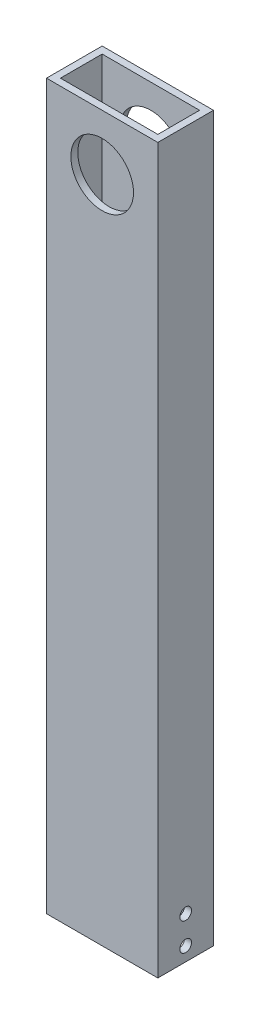
SolidWorks part; units mm, degrees
ref_plane "Front Plane" through (0, 0, 0) normal (0, 0, 1) x (1, 0, 0)
ref_plane "Top Plane" through (0, 0, 0) normal (0, 1, 0) x (1, 0, 0)
ref_plane "Right Plane" through (0, 0, 0) normal (1, 0, 0) x (0, 0, -1)
sketch "Sketch1" plane through (0, 0, 0) normal (0, 1, 0) x (1, 0, 0)
  line L1 (0, 0) -> (50.8, 0)
  line L2 (0, 0) -> (0, 25.4)
  line L3 (0, 25.4) -> (50.8, 25.4)
  line L4 (50.8, 0) -> (50.8, 25.4)
  line L5 (3.175, 3.175) -> (47.625, 3.175)
  line L6 (3.175, 3.175) -> (3.175, 22.225)
  line L7 (3.175, 22.225) -> (47.625, 22.225)
  line L8 (47.625, 3.175) -> (47.625, 22.225)
  dimension "D1" = 3.175
  dimension "D2" = 3.175
  dimension "D3" = 3.175
  dimension "D4" = 3.175
  dimension "D5" = 25.4
  dimension "D6" = 50.8
extrude "Boss-Extrude2" add sketch "Sketch1" along normal blind 330.2
sketch "Sketch2" plane through (0, 0, 0) normal (0, 0, 1) x (1, 0, 0)
  line L0 (0, 330.2) -> (0, 0) construction
  line L1 (0, 330.2) -> (50.8, 330.2) construction
  circle A0 centre (25.4, 304.8) radius 14.2875
  dimension "D3" = 28.575
  dimension "D1" = 25.4
  dimension "D2" = 25.4
extrude "Cut-Extrude1" cut sketch "Sketch2" against normal up to surface (25.4 mm away) contours A0 up to face at (25.4, 165.1, -25.4)
sketch "Sketch3" plane through (50.8, 0, 0) normal (1, 0, 0) x (0, 0, -1)
  line L0 (0, 0) -> (25.4, 0) construction
  line L2 (0, 330.2) -> (0, 0) construction
  circle A0 centre (12.7, 19.05) radius 2.667
  circle A1 centre (12.7, 6.35) radius 2.667
  dimension "D2" = 6.35
  dimension "D3" = 12.7
  dimension "D4" = 12.7
  dimension "D5" = 5.334
  dimension "D6" = 5.334
  dimension "D1" = 12.7
extrude "Cut-Extrude2" cut sketch "Sketch3" against normal up to surface (3.175 mm away) up to face at (47.625, 165.1, -12.7)
